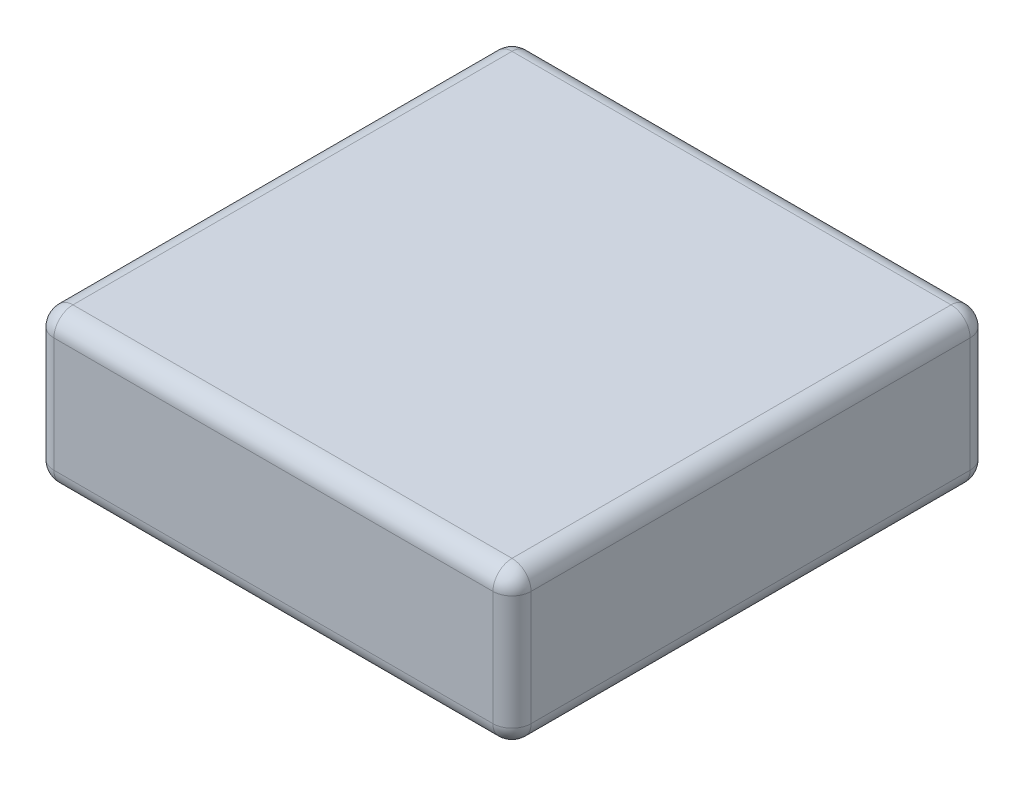
SolidWorks part; units mm, degrees
material "Duranickel(R) 301"
ref_plane "Front Plane" through (0, 0, 0) normal (0, 0, 1) x (1, 0, 0)
ref_plane "Top Plane" through (0, 0, 0) normal (0, 1, 0) x (1, 0, 0)
ref_plane "Right Plane" through (0, 0, 0) normal (1, 0, 0) x (0, 0, -1)
sketch "Sketch1" plane through (0, 0, 0) normal (0, 1, 0) x (1, 0, 0)
  line L1 (12.5, -12.5) -> (-12.5, -12.5)
  line L2 (12.5, -12.5) -> (12.5, 12.5)
  line L3 (12.5, 12.5) -> (-12.5, 12.5)
  line L4 (-12.5, -12.5) -> (-12.5, 12.5)
  line L5 (12.5, -12.5) -> (-12.5, 12.5) construction
  line L6 (12.5, 12.5) -> (-12.5, -12.5) construction
  point P0 (0, 0)
  dimension "D1" = 25
  dimension "D2" = 25
extrude "Base" add sketch "Sketch1" along normal blind 8
fillet "Fillet1" radius 1 12 edges at (0, 0, 12.5) (12.5, 0, 0) (0, 0, -12.5) (-12.5, 0, 0) (0, 8, -12.5) (12.5, 8, 0) (0, 8, 12.5) (-12.5, 8, 0) (-12.5, 4, 12.5) (-12.5, 4, -12.5) (12.5, 4, 12.5) (12.5, 4, -12.5)
equation "\"D2@Sketch1\"=\"D1@Sketch1\""
